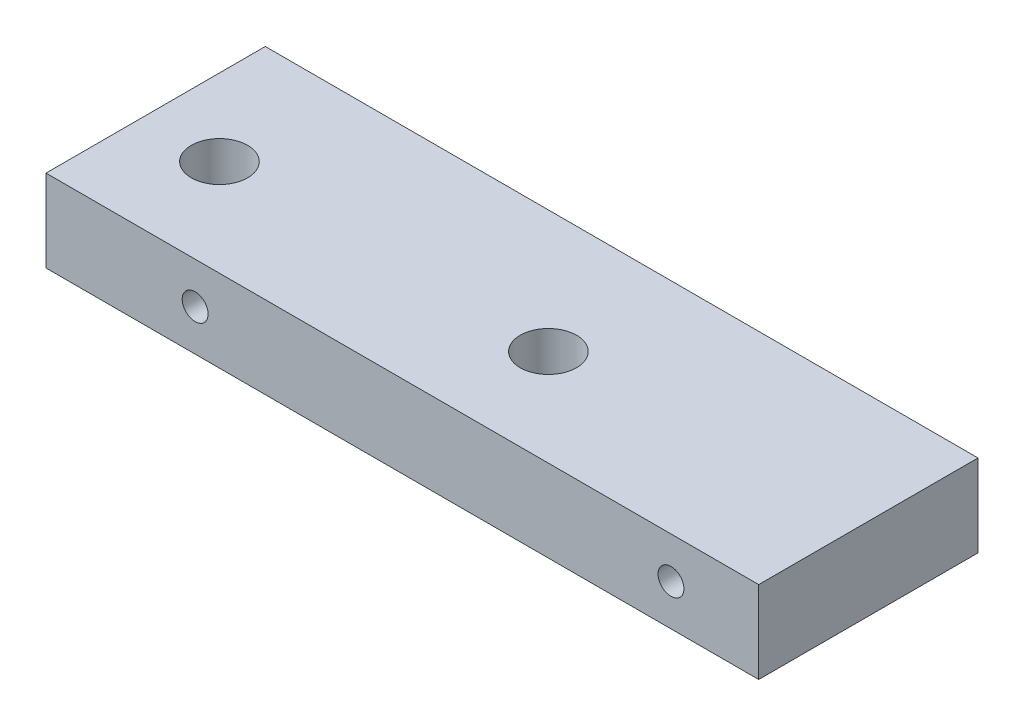
SolidWorks part; units mm, degrees
material "6061-T6 (SS)"
ref_plane "Front Plane" through (0, 0, 0) normal (0, 0, 1) x (1, 0, 0)
ref_plane "Top Plane" through (0, 0, 0) normal (0, 1, 0) x (1, 0, 0)
ref_plane "Right Plane" through (0, 0, 0) normal (1, 0, 0) x (0, 0, -1)
sketch "Sketch1" plane through (0, 0, 0) normal (0, 1, 0) x (1, 0, 0)
  line L1 (0, 0) -> (-82.55, 0)
  line L2 (0, 0) -> (0, -25.4)
  line L3 (0, -25.4) -> (-82.55, -25.4)
  line L4 (-82.55, 0) -> (-82.55, -25.4)
  dimension "D1" = 82.55
  dimension "D2" = 25.4
extrude "Boss-Extrude1" add sketch "Sketch1" along normal blind 9.525
hole_wizard "1/4 Clearance Hole1" positions "Sketch12" profile "Sketch13" hole size "1/4" standard "ANSI Inch" end condition through all
sketch "Sketch12" plane through (0, 9.525, 0) normal (0, 1, 0) x (1, 0, 0)
  line L0 (0, -25.4) -> (0, 0) construction
  line L2 (-82.55, -25.4) -> (0, -25.4) construction
  point P0 (-73.66, -14.2)
  point P5 (0, -12.7)
  point P11 (-35.56, -14.2)
  dimension "D1" = 73.66
  dimension "D2" = 11.2
  dimension "D3" = 38.1
sketch "Sketch13" plane through (-73.66, 9.525, 14.2) normal (1, 0, 0) x (0, 0, 1)
  line L0 (0, 0) -> (0, 9.525)
  line L1 (0, 9.525) -> (3.2639, 9.525)
  line L2 (3.2639, 9.525) -> (3.2639, 0)
  line L5 (3.2639, 0) -> (0, 0)
  line L11 (0, -6.35) -> (0, 107.95) construction
  dimension "Thru Hole Dia." = 6.5278
  dimension "Thru Hole Depth" = 9.525
sketch "Sketch15" plane through (0, 0, 25.4) normal (0, 0, 1) x (1, 0, 0)
  line L0 (0, 9.525) -> (0, 0) construction
  line L1 (-82.55, 9.525) -> (-82.55, 0) construction
  circle A1 centre (-65.278, 4.7625) radius 1.5
  circle A2 centre (-10.16, 4.7625) radius 1.5
  point P0 (-65.278, 4.7625)
  point P2 (-10.16, 4.7625)
  point P12 (-82.55, 4.7625)
  dimension "D3" = 3
  dimension "D1" = 10.16
  dimension "D2" = 55.118
extrude "Cut-Extrude1" cut sketch "Sketch15" against normal through all
sketch "Sketch16" plane through (0, 0, 25.4) normal (0, 0, 1) x (1, 0, 0)
  circle A1 centre (-65.278, 4.7625) radius 2.75
  circle A2 centre (-10.16, 4.7625) radius 2.75
  dimension "D1" = 5.5
